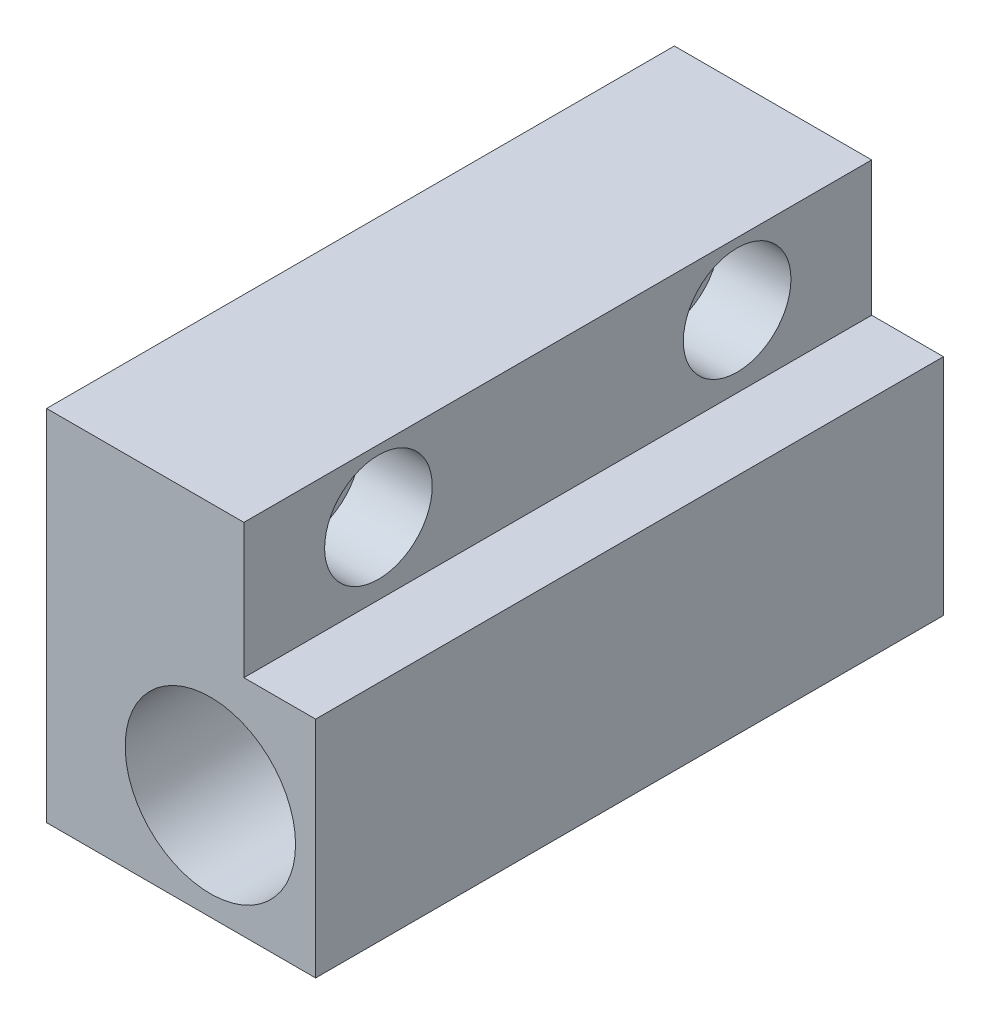
SolidWorks part; units mm, degrees
ref_plane "前视基准面" through (0, 0, 0) normal (0, 0, 1) x (1, 0, 0)
ref_plane "上视基准面" through (0, 0, 0) normal (0, 1, 0) x (1, 0, 0)
ref_plane "右视基准面" through (0, 0, 0) normal (1, 0, 0) x (0, 0, -1)
sketch "草图1" plane through (0, 0, 0) normal (0, 0, 1) x (1, 0, 0)
  line L1 (32.8476, 30.8429) -> (62.8476, 30.8429)
  line L2 (32.8476, 30.8429) -> (32.8476, -9.1571)
  line L3 (32.8476, -9.1571) -> (62.8476, -9.1571)
  line L4 (62.8476, 30.8429) -> (62.8476, -9.1571)
  dimension "D1" = 30
  dimension "D2" = 40
extrude "凸台-拉伸1" add sketch "草图1" along normal blind 70
sketch "草图2" plane through (0, 0, 70) normal (0, 0, 1) x (1, 0, 0)
  circle A0 centre (51.1072, 2.6082) radius 9.5
  dimension "D1" = 19
sketch "草图3" plane through (62.8476, 0, 0) normal (1, 0, 0) x (0, 0, -1)
  line L2 (-70, 30.8429) -> (0, 30.8429) construction
  circle A0 centre (-55, 23.8429) radius 3
  circle A1 centre (-15, 23.8429) radius 3
  dimension "D1" = 6
  dimension "D2" = 6
  dimension "D3" = 7
  dimension "D4" = 7
extrude "切除-拉伸1" cut sketch "草图3" against normal blind 70
sketch "草图4" plane through (62.8476, 0, 0) normal (1, 0, 0) x (0, 0, -1)
  circle A0 centre (-55, 23.8429) radius 6
  circle A1 centre (-15, 23.8429) radius 6
  dimension "D1" = 12
  dimension "D2" = 12
extrude "切除-拉伸2" cut sketch "草图4" against normal blind 16
sketch "草图5" plane through (0, 0, 70) normal (0, 0, 1) x (1, 0, 0)
  line L0 (62.8476, 30.8429) -> (32.8476, 30.8429) construction
  line L1 (54.8476, 30.8429) -> (62.8476, 30.8429)
  line L2 (54.8476, 30.8429) -> (54.8476, 15.8429)
  line L3 (54.8476, 15.8429) -> (62.8476, 15.8429)
  line L4 (62.8476, 30.8429) -> (62.8476, 15.8429)
  line L5 (62.8476, -9.1571) -> (62.8476, 30.8429) construction
  line L6 (46.8476, 17.8429) -> (46.8476, 29.8429) construction
  line L7 (46.8476, 17.8429) -> (62.8476, 17.8429) construction
  dimension "D1" = 8
  dimension "D2" = 2
extrude "切除-拉伸3" cut sketch "草图5" against normal blind 75
extrude "切除-拉伸4" cut sketch "草图2" against normal blind 60
sketch "草图6" plane through (0, 0, 10) normal (0, 0, 1) x (1, 0, 0)
  circle A0 centre (51.1072, 2.6082) radius 5
  dimension "D1" = 10
extrude "切除-拉伸5" cut sketch "草图6" against normal blind 50
